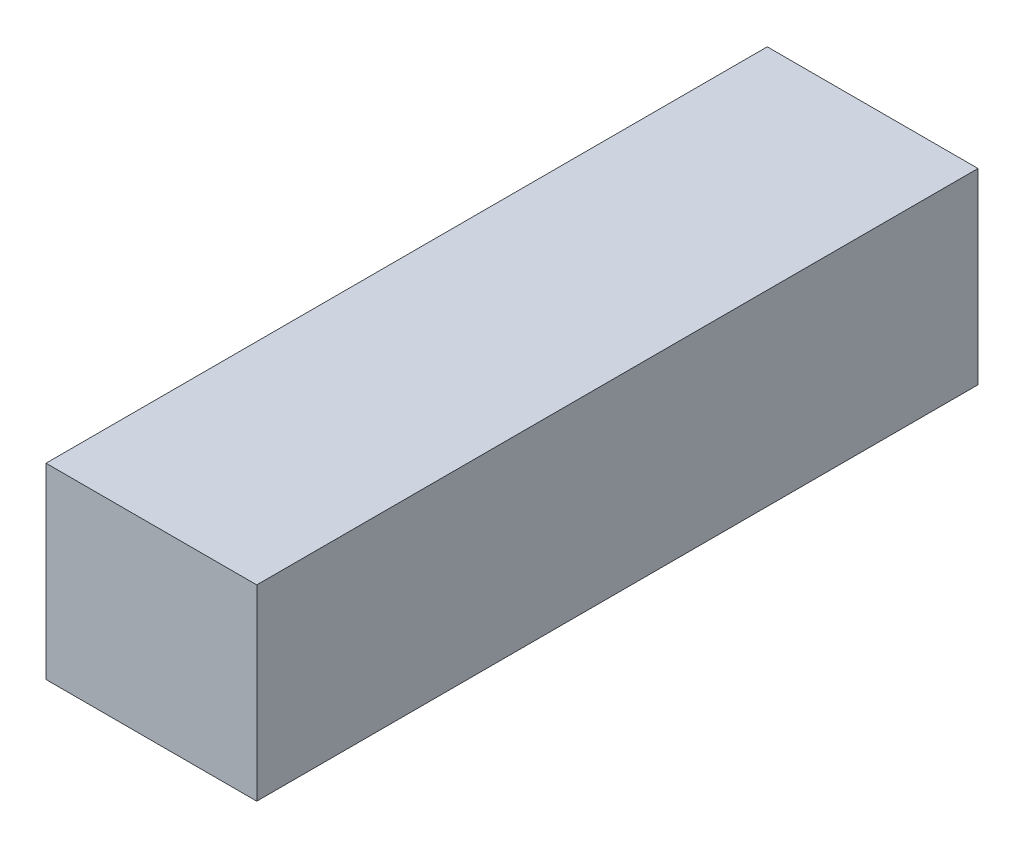
SolidWorks part; units mm, degrees
ref_plane "Front Plane" through (0, 0, 0) normal (0, 0, 1) x (1, 0, 0)
ref_plane "Top Plane" through (0, 0, 0) normal (0, 1, 0) x (1, 0, 0)
ref_plane "Right Plane" through (0, 0, 0) normal (1, 0, 0) x (0, 0, -1)
sketch "Sketch1" plane through (0, 0, 0) normal (0, 0, 1) x (1, 0, 0)
  line L1 (-22.5, -20) -> (22.5, -20)
  line L2 (-22.5, -20) -> (-22.5, 20)
  line L3 (-22.5, 20) -> (22.5, 20)
  line L4 (22.5, -20) -> (22.5, 20)
  line L5 (-22.5, -20) -> (22.5, 20) construction
  line L6 (-22.5, 20) -> (22.5, -20) construction
  point P0 (0, 0)
  dimension "D1" = 40
  dimension "D2" = 45
extrude "Boss-Extrude1" add sketch "Sketch1" along normal blind 154
